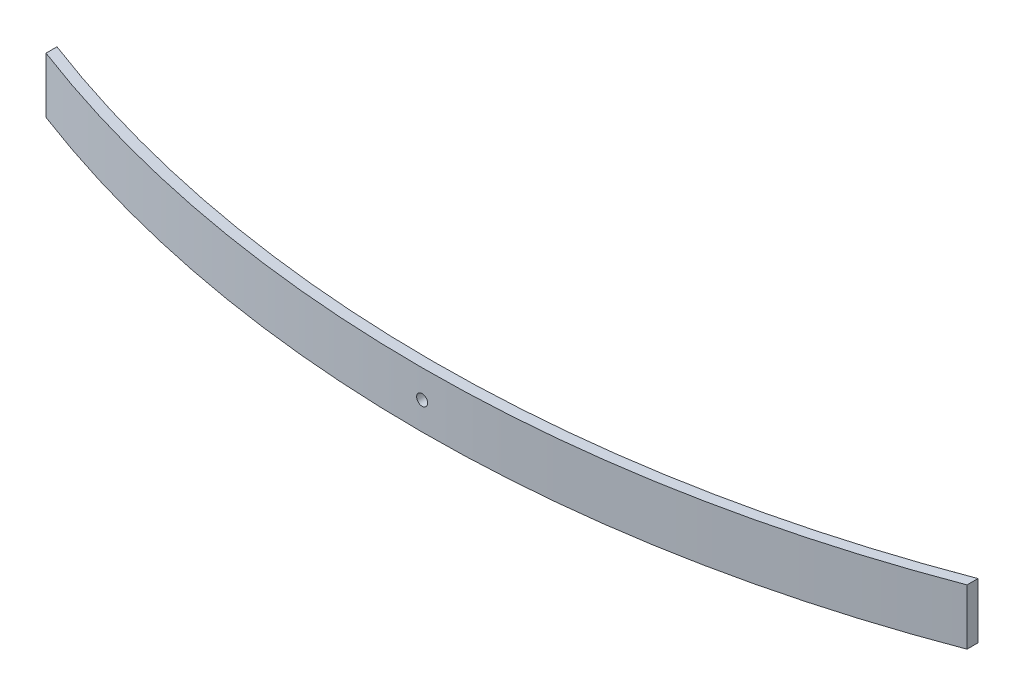
SolidWorks part; units mm, degrees
ref_plane "Front Plane" through (0, 0, 0) normal (0, 0, 1) x (1, 0, 0)
ref_plane "Top Plane" through (0, 0, 0) normal (0, 1, 0) x (1, 0, 0)
ref_plane "Right Plane" through (0, 0, 0) normal (1, 0, 0) x (0, 0, -1)
sketch "Sketch1" plane through (0, 0, 0) normal (0, 1, 0) x (1, 0, 0)
  line L0 (-630, 0) -> (630, 0) construction
  line L1 (-210.8013, -133) -> (245.5549, -133) construction
  line L2 (0, 0) -> (0, -133) construction
  line L3 (-602.5798, 17.4465) -> (-589.9243, 25.4988)
  line L4 (-616.835, -11.5296) -> (-605.5506, -21.4121)
  line L5 (616.835, -11.5296) -> (605.5506, -21.4121)
  line L6 (-630.0217, -47.5) -> (-630.0217, -62.5)
  line L7 (602.5798, 17.4465) -> (589.9243, 25.4988)
  line L8 (630.0217, -47.5) -> (630.0217, -62.5)
  arc A0 (-616.835, -11.5296) -> (-630, -17.5) centre (-630, 0) ccw
  arc A1 (630, -17.5) -> (616.835, -11.5296) centre (630, 0) ccw
  arc A2 (-630, -17.5) -> (630, -17.5) centre (0, 1642.9318) ccw
  arc A3 (-630.0011, -32.5) -> (630.0011, -32.5) centre (0, 1627.9379) ccw
  arc A4 (-605.5506, -21.4121) -> (-630.0011, -32.5) centre (-630, 0) ccw
  arc A5 (630.0011, -32.5) -> (605.5506, -21.4121) centre (630, 0) ccw
  arc A6 (-630.0217, -47.5) -> (630.0217, -47.5) centre (0, 1613.05) ccw
  arc A7 (630.0217, -47.5) -> (589.9243, 25.4988) centre (630, 0) ccw
  arc A8 (-589.9243, 25.4988) -> (-630.0217, -47.5) centre (-630, 0) ccw
  arc A9 (-630.0217, -62.5) -> (630.0217, -62.5) centre (0, 1598.05) ccw
  point P5 (-630.0217, -47.5)
  point P6 (0, -163)
  point P10 (0, -133)
  point P13 (-630.0011, -32.5)
  point P14 (0, -148)
  point P15 (630.0011, -32.5)
  point P20 (630.0217, -47.5)
  point P27 (0, -178)
  dimension "D4" = 35
  dimension "D5" = 35
  dimension "D9" = 15
  dimension "D12" = 15
  dimension "D1" = 133
  dimension "D2" = 630
  dimension "D3" = 630
  dimension "D6" = 15
  dimension "D7" = 15
  dimension "D8" = 15
  dimension "D10" = 15
  dimension "D11" = 15
  dimension "D13" = 15
  dimension "D14" = 15
sketch "Sketch5" plane through (0, 0, 0) normal (0, 0, 1) x (1, 0, 0)
  circle A0 centre (0, 38.1) radius 7.5
  dimension "D2" = 15
  dimension "D1" = 38.1
sketch "Sketch6" plane through (0, 0, 0) normal (0, 0, 1) x (1, 0, 0)
  circle A0 centre (0, 38.1) radius 7.5
extrude "Boss-Extrude1" add sketch "Sketch1" along normal blind 76.2 contours L6 A9 L8 A6
sketch "Sketch7" plane through (0, 0, 0) normal (0, 0, 1) x (1, 0, 0)
  circle A0 centre (0, 38.1) radius 7.5
extrude "Cut-Extrude1" cut sketch "Sketch7" along normal through all
